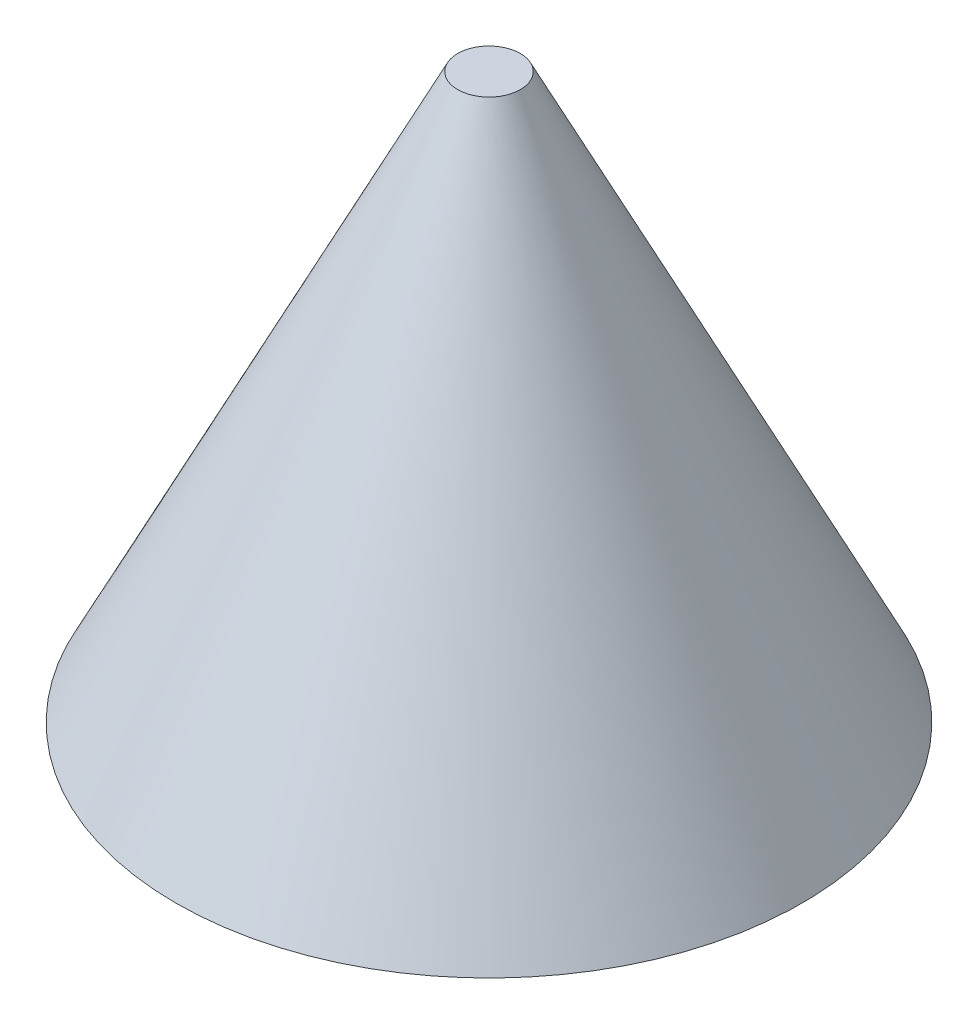
SolidWorks part; units mm, degrees
ref_plane "前视基准面" through (0, 0, 0) normal (0, 0, 1) x (1, 0, 0)
ref_plane "上视基准面" through (0, 0, 0) normal (0, 1, 0) x (1, 0, 0)
ref_plane "右视基准面" through (0, 0, 0) normal (1, 0, 0) x (0, 0, -1)
sketch "草图1" plane through (0, 0, 0) normal (0, 0, 1) x (1, 0, 0)
  line L0 (0, 0) -> (5, 0)
  line L1 (0, 0) -> (0, 10)
  line L2 (0, 10) -> (5, 0)
revolve "旋转1" add sketch "草图1" angle 360 about L1
sketch "草图2" plane through (0, 0, 0) normal (0, -1, 0) x (1, 0, 0)
  circle A0 centre (0, 0) radius 0.5
extrude "切除-拉伸1" cut sketch "草图2" against normal blind 10 from offset 9 offset against normal yes
sketch "草图3" plane through (0, 0, 0) normal (0, -1, 0) x (1, 0, 0)
  circle A0 centre (0, 0) radius 2.5
extrude "切除-拉伸2" cut sketch "草图3" against normal blind 3
